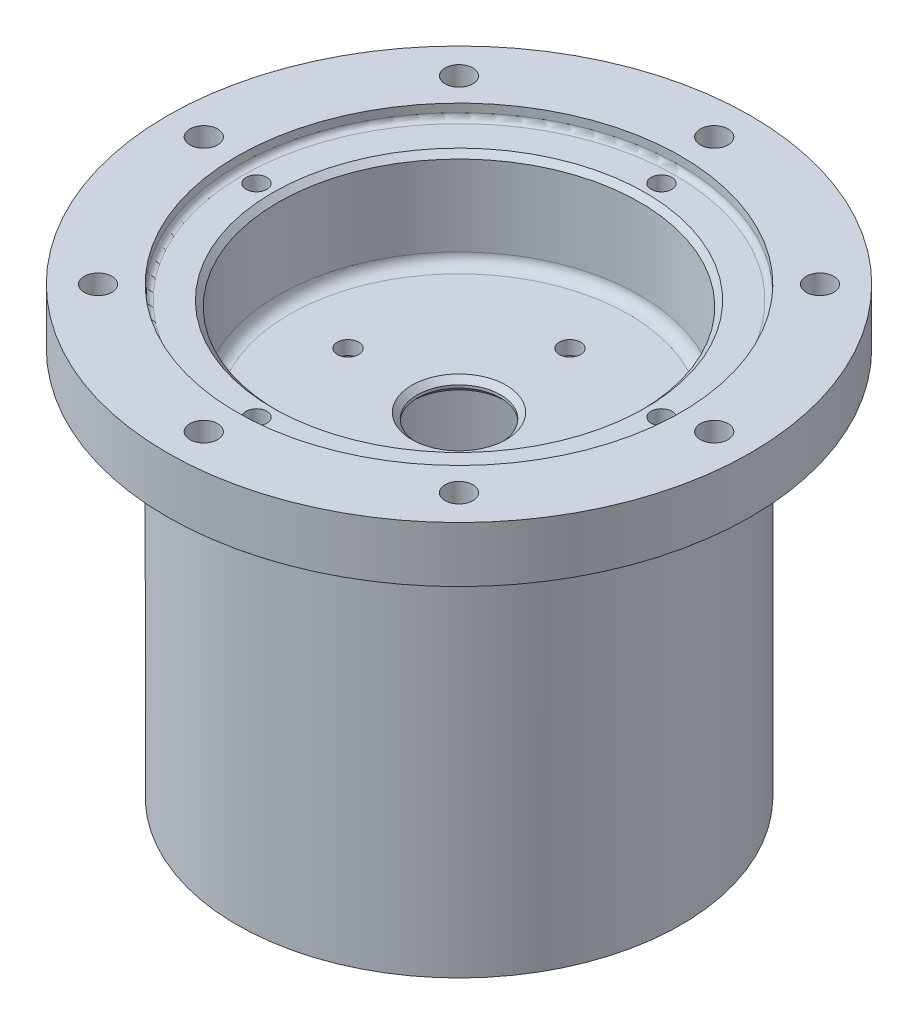
SolidWorks part; units mm, degrees
ref_plane "Front Plane" through (0, 0, 0) normal (0, 0, 1) x (1, 0, 0)
ref_plane "Top Plane" through (0, 0, 0) normal (0, 1, 0) x (1, 0, 0)
ref_plane "Right Plane" through (0, 0, 0) normal (1, 0, 0) x (0, 0, -1)
sketch "Sketch1" plane through (0, 0, 0) normal (0, 0, 1) x (1, 0, 0)
  line L0 (0, 50.8) -> (0, -50.8) construction
  line L2 (-66.802, 50.8) -> (-66.802, 38.1)
  line L3 (-66.802, 38.1) -> (-50.8, 38.1)
  line L4 (-50.8, 38.1) -> (-50.8, -50.8)
  line L5 (-50.8, -50.8) -> (-41.402, -50.8)
  line L6 (-41.402, -50.8) -> (-41.402, 22.225)
  line L7 (-41.402, 22.225) -> (-9.525, 22.225)
  line L8 (-9.525, 22.225) -> (-9.525, 25.4)
  line L9 (-9.525, 25.4) -> (-41.402, 25.4)
  line L13 (-50.8, 50.8) -> (-50.8, 47.625)
  line L14 (-50.8, 47.625) -> (-41.402, 47.625)
  line L15 (-66.802, 50.8) -> (-50.8, 50.8)
  line L16 (-41.402, 47.625) -> (-41.402, 25.4)
  point P3 (0, 0)
  dimension "D1" = 101.6
  dimension "D2" = 66.802
  dimension "D3" = 9.525
  dimension "D4" = 3.175
  dimension "D5" = 3.175
  dimension "D6" = 25.4
  dimension "D7" = 41.402
  dimension "D8" = 50.8
  dimension "D9" = 101.6
  dimension "D10" = 50.8
  dimension "D11" = 12.7
revolve "Revolve1" add sketch "Sketch1" angle 360 about L0
hole_wizard "#10 (0.1935) Diameter Hole1" positions "Sketch10" profile "Sketch11" hole size "#10" standard "ANSI Inch" end condition through all
sketch "Sketch10" plane through (0, 25.4, 0) normal (0, 1, 0) x (1, 0, 0)
  point P0 (0, 25.4)
  point P2 (25.4, 0)
  point P4 (0, -25.4)
  point P6 (-25.4, 0)
  point P10 (0, 0)
  dimension "D1" = 25.4
  dimension "D2" = 25.4
  dimension "D3" = 25.4
  dimension "D4" = 25.4
sketch "Sketch11" plane through (0, 25.4, -25.4) normal (1, 0, 0) x (0, 0, 1)
  line L0 (0, 0) -> (0, 76.2)
  line L1 (0, 76.2) -> (2.4574, 76.2)
  line L2 (2.4574, 76.2) -> (2.4574, 0)
  line L5 (2.4574, 0) -> (0, 0)
  line L11 (0, -6.35) -> (0, 107.95) construction
  dimension "Thru Hole Dia." = 4.9149
  dimension "Thru Hole Depth" = 76.2
hole_wizard "3/16 (0.1875) Diameter Hole1" positions "Sketch12" profile "Sketch13" hole size "3/16" standard "ANSI Inch"
sketch "Sketch12" plane through (0, 47.625, 0) normal (0, 1, 0) x (1, 0, 0)
  point P0 (0, 46.355)
  point P2 (46.355, 0)
  point P4 (0, -46.355)
  point P6 (-46.355, 0)
  point P10 (0, 0)
  point P11 (0, 0)
  point P12 (0, 0)
  dimension "D1" = 46.355
  dimension "D2" = 46.355
  dimension "D3" = 46.355
  dimension "D4" = 46.355
sketch "Sketch13" plane through (0, 47.625, -46.355) normal (1, 0, 0) x (0, 0, 1)
  line L0 (0, 0) -> (0, 7.7808)
  line L1 (0, 7.7808) -> (2.3812, 6.35)
  line L2 (2.3812, 6.35) -> (2.3812, 0)
  line L5 (2.3812, 0) -> (0, 0)
  line L10 (0, 7.7808) -> (-2.3812, 6.35) construction
  line L11 (0, -6.35) -> (0, 107.95) construction
  dimension "Hole Dia." = 4.7625
  dimension "Hole Depth" = 6.35
  dimension "Drill Angle" = 118
fillet "Fillet1" radius 2.54 3 edges at (-41.402, 25.4, 0) (-41.402, 22.225, 0) (-50.8, 38.1, 0)
fillet "Fillet2" radius 1.27 1 edges at (-50.8, 47.625, 0)
chamfer "Chamfer1" distance 1.27 angle 45 3 edges at (-9.525, 22.225, 0) (-9.525, 25.4, 0) (-41.402, 47.625, 0)
hole_wizard "1/4 (0.25) Diameter Hole2" positions "Sketch17" profile "Sketch18" hole size "1/4" standard "ANSI Inch"
sketch "Sketch17" plane through (0, 50.8, 0) normal (0, 1, 0) x (1, 0, 0)
  point P0 (0, 58.42)
  point P8 (41.3092, 41.3092)
  point P9 (58.42, 0)
  point P10 (41.3092, -41.3092)
  point P11 (0, -58.42)
  point P12 (-41.3092, -41.3092)
  point P13 (-58.42, 0)
  point P14 (-41.3092, 41.3092)
  point P15 (0, 0)
  dimension "D1" = 58.42
  dimension "D2" = 8
sketch "Sketch18" plane through (0, 50.8, -58.42) normal (1, 0, 0) x (0, 0, 1)
  line L0 (0, 0) -> (0, 14.6077)
  line L1 (0, 14.6077) -> (3.175, 12.7)
  line L2 (3.175, 12.7) -> (3.175, 0)
  line L5 (3.175, 0) -> (0, 0)
  line L10 (0, 14.6077) -> (-3.175, 12.7) construction
  line L11 (0, -6.35) -> (0, 107.95) construction
  dimension "Hole Dia." = 6.35
  dimension "Hole Depth" = 12.7
  dimension "Drill Angle" = 118
sketch "Sketch19" plane through (0, 50.8, 0) normal (0, 1, 0) x (1, 0, 0)
  line L0 (0, 0) -> (-58.42, 0) construction
  line L1 (-53.973, -22.3564) -> (0, 0) construction
  circle A0 centre (-53.973, -22.3564) radius 3.175
  dimension "D2" = 6.35
  dimension "D1" = 22.5
  dimension "D3" = 58.42
